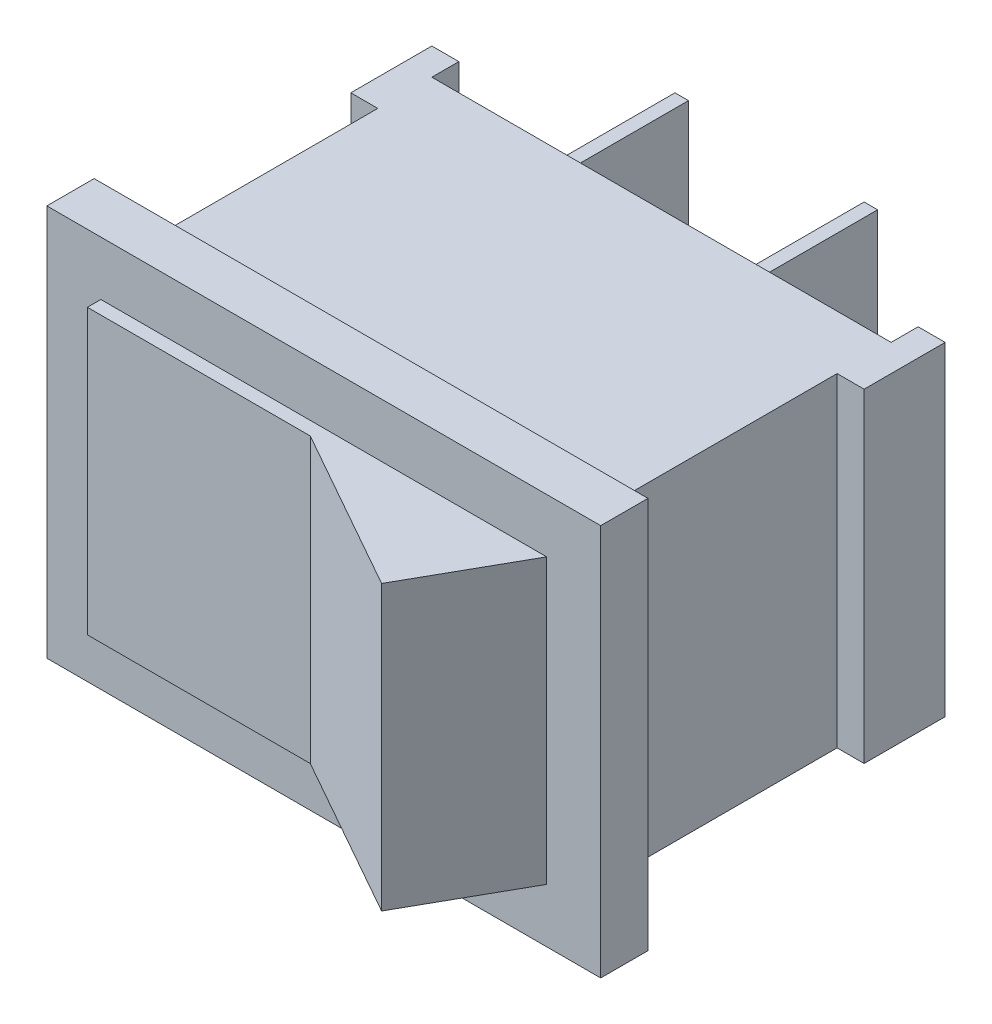
SolidWorks part; units mm, degrees
ref_plane "Piano frontale" through (0, 0, 0) normal (0, 0, 1) x (1, 0, 0)
ref_plane "Piano superiore" through (0, 0, 0) normal (0, 1, 0) x (1, 0, 0)
ref_plane "Piano destro" through (0, 0, 0) normal (1, 0, 0) x (0, 0, -1)
sketch "Schizzo1" plane through (0, 0, 0) normal (0, 0, 1) x (1, 0, 0)
  line L1 (10.25, -7.25) -> (-10.25, -7.25)
  line L2 (10.25, -7.25) -> (10.25, 7.25)
  line L3 (10.25, 7.25) -> (-10.25, 7.25)
  line L4 (-10.25, -7.25) -> (-10.25, 7.25)
  line L5 (10.25, -7.25) -> (-10.25, 7.25) construction
  line L6 (10.25, 7.25) -> (-10.25, -7.25) construction
  point P0 (0, 0)
  dimension "D1" = 20.5
  dimension "D2" = 14.5
extrude "Estrusione-Estrusione1" add sketch "Schizzo1" along normal blind 1.75
sketch "Schizzo2" plane through (0, 0, 0) normal (0, 0, -1) x (-1, 0, 0)
  line L1 (8.5, -6) -> (-8.5, -6)
  line L2 (8.5, -6) -> (8.5, 6)
  line L3 (8.5, 6) -> (-8.5, 6)
  line L4 (-8.5, -6) -> (-8.5, 6)
  line L5 (8.5, -6) -> (-8.5, 6) construction
  line L6 (8.5, 6) -> (-8.5, -6) construction
  point P0 (0, 0)
  dimension "D1" = 12
  dimension "D2" = 17
extrude "Estrusione-Estrusione2" add sketch "Schizzo2" along normal blind 10.75
sketch "Schizzo3" plane through (8.5, 0, 0) normal (1, 0, 0) x (0, 0, -1)
  line L0 (10.75, 6) -> (0, 6) construction
  line L1 (8.75, 6) -> (11.75, 6)
  line L2 (8.75, 6) -> (8.75, -6)
  line L3 (8.75, -6) -> (11.75, -6)
  line L4 (11.75, 6) -> (11.75, -6)
  line L5 (10.75, 6) -> (10.75, -6) construction
  dimension "D1" = 2
  dimension "D2" = 1
extrude "Estrusione-Estrusione3" add sketch "Schizzo3" along normal blind 1
sketch "Schizzo4" plane through (-8.5, 0, 0) normal (-1, 0, 0) x (0, 0, 1)
  line L0 (-10.75, 6) -> (0, 6) construction
  line L1 (-8.75, 6) -> (-11.75, 6)
  line L2 (-8.75, 6) -> (-8.75, -6)
  line L3 (-8.75, -6) -> (-11.75, -6)
  line L4 (-11.75, 6) -> (-11.75, -6)
  line L5 (-10.75, -6) -> (-10.75, 6) construction
  dimension "D1" = 2
extrude "Estrusione-Estrusione4" add sketch "Schizzo4" along normal blind 1
sketch "Schizzo6" plane through (0, 0, 1.75) normal (0, 0, 1) x (1, 0, 0)
  line L0 (10.25, 7.25) -> (-10.25, 7.25) construction
  line L1 (0, 5.25) -> (-8.25, 5.25)
  line L2 (0, 5.25) -> (0, -5.25)
  line L3 (0, -5.25) -> (-8.25, -5.25)
  line L4 (-8.25, 5.25) -> (-8.25, -5.25)
  line L5 (-10.25, 7.25) -> (-10.25, -7.25) construction
  line L6 (-10.25, -7.25) -> (10.25, -7.25) construction
  dimension "D1" = 2
  dimension "D2" = 2
  dimension "D3" = 2
extrude "Estrusione-Estrusione5" add sketch "Schizzo6" along normal blind 0.5
sketch "Schizzo8" plane through (0, 5.25, 0) normal (0, 1, 0) x (1, 0, 0)
  line L0 (0, -2.25) -> (6.0484, -5.6577)
  line L1 (6.0484, -5.6577) -> (8.25, -1.75)
  line L2 (10.25, -1.75) -> (-10.25, -1.75) construction
  line L3 (8.25, -1.75) -> (0, -1.75)
  line L4 (0, -1.75) -> (0, -2.25)
  dimension "D1" = 8.25
extrude "Estrusione-Estrusione6" add sketch "Schizzo8" against normal up to surface (10.5 mm away) up to face at (-4.125, -5.25, 2)
sketch "Schizzo9" plane through (0, 0, -10.75) normal (0, 0, -1) x (-1, 0, 0)
  line L0 (-8.5, 0) -> (8.5, 0) construction
  line L1 (-8.5, -6) -> (-8.5, 6) construction
  line L2 (8.5, 6) -> (8.5, -6) construction
  line L3 (9.5, 6) -> (9.5, -6) construction
  line L4 (7.5, -2) -> (7, -2)
  line L5 (7.5, -2) -> (7.5, 2)
  line L6 (7.5, 2) -> (7, 2)
  line L7 (7, -2) -> (7, 2)
  line L8 (7.5, -2) -> (7, 2) construction
  line L9 (7.5, 2) -> (7, -2) construction
  line L11 (0, -2) -> (0.5, -2)
  line L12 (0, -2) -> (0, 2)
  line L13 (0, 2) -> (0.5, 2)
  line L14 (0.5, -2) -> (0.5, 2)
  line L15 (0, -2) -> (0.5, 2) construction
  line L16 (0, 2) -> (0.5, -2) construction
  point P6 (7.25, 0)
  point P13 (0.25, 0)
  dimension "D1" = 2
  dimension "D2" = 0.5
  dimension "D3" = 4
  dimension "D4" = 6.5
  dimension "D5" = 0.5
  dimension "D6" = 4
extrude "Estrusione-Estrusione7" add sketch "Schizzo9" along normal blind 8
sketch "Schizzo10" plane through (0, -6, 0) normal (0, -1, 0) x (1, 0, 0)
  line L0 (0, 0) -> (0, -10.75) construction
  line L1 (8.5, 0) -> (-8.5, 0) construction
  line L2 (8.5, -10.75) -> (-8.5, -10.75) construction
